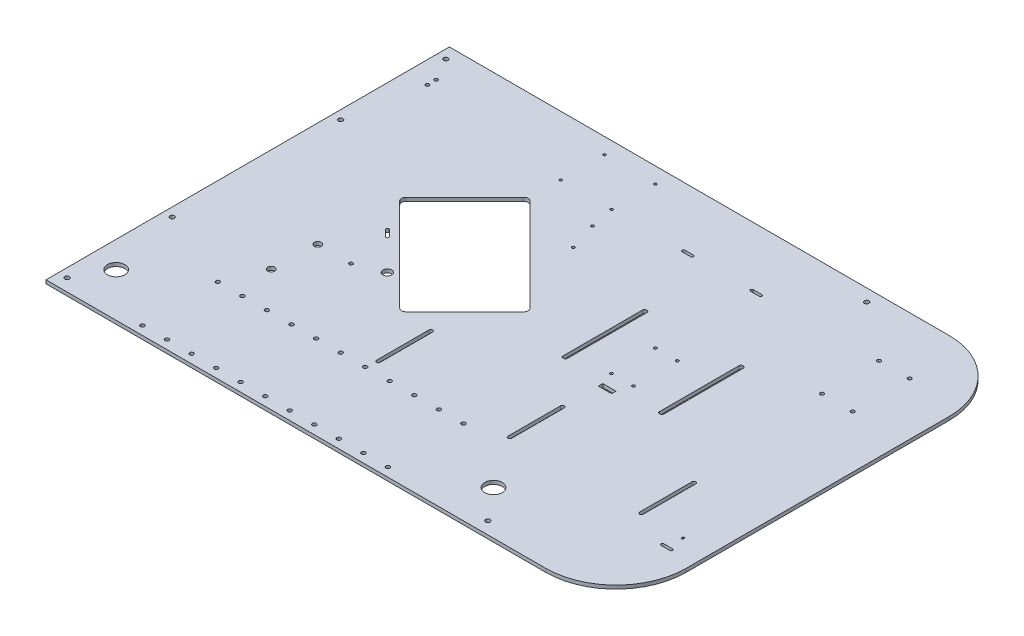
SolidWorks part; units mm, degrees
ref_plane "前视基准面" through (0, 0, 0) normal (0, 0, 1) x (1, 0, 0)
ref_plane "上视基准面" through (0, 0, 0) normal (0, 1, 0) x (1, 0, 0)
ref_plane "右视基准面" through (0, 0, 0) normal (1, 0, 0) x (0, 0, -1)
sketch "草图1" plane through (0, 0, 0) normal (0, 1, 0) x (1, 0, 0)
  line L1 (-325, 230) -> (325, 230)
  line L2 (-325, 230) -> (-325, -230)
  line L3 (-325, -230) -> (325, -230)
  line L4 (325, 230) -> (325, -230)
  line L5 (-325, 230) -> (325, -230) construction
  line L6 (-325, -230) -> (325, 230) construction
  point P0 (0, 0)
  dimension "D1" = 650
  dimension "D2" = 460
extrude "凸台-拉伸1" add sketch "草图1" along normal blind 4
sketch "草图2" plane through (0, 4, 0) normal (0, 1, 0) x (1, 0, 0)
  line L0 (325, -110) -> (145.735, -110) construction
  line L1 (325, -230) -> (325, 230) construction
  line L2 (288.7, -75) -> (319, -75) construction
  line L3 (-325, -230) -> (325, -230) construction
  line L4 (-152.45, -61.9939) -> (-152.45, -234.8498) construction
  line L5 (-241.4703, -110) -> (-123.3197, -110) construction
  circle A0 centre (319, -145) radius 2
  circle A1 centre (288.7, -145) radius 2
  circle A2 centre (319, -75) radius 2
  circle A3 centre (288.7, -75) radius 2
  circle A5 centre (-138.045, -75) radius 1.6
  circle A6 centre (-166.855, -75) radius 1.6
  circle A7 centre (-138.045, -145) radius 1.6
  circle A8 centre (-166.855, -145) radius 1.6
  dimension "D1" = 4
  dimension "D2" = 4
  dimension "D8" = 28.81
  dimension "D3" = 30.3
  dimension "D4" = 6
  dimension "D5" = 70
  dimension "D6" = 120
  dimension "D7" = 477.45
  dimension "D9" = 70
sketch "草图3" plane through (0, 4, 0) normal (0, 1, 0) x (1, 0, 0)
  line L0 (325, -230) -> (325, 230) construction
  line L1 (325, 230) -> (-325, 230) construction
  line L2 (230, 165) -> (265, 165) construction
  line L3 (230, 100) -> (265, 100) construction
  line L4 (230, 165) -> (230, 100) construction
  circle A0 centre (230, 165) radius 2.05
  circle A1 centre (265, 165) radius 2.05
  circle A2 centre (265, 100) radius 2.05
  circle A3 centre (230, 100) radius 2.05
  dimension "D1" = 4.1
  dimension "D2" = 4.1
  dimension "D3" = 4.1
  dimension "D4" = 4.1
  dimension "D5" = 35
  dimension "D6" = 65
  dimension "D7" = 35
  dimension "D8" = 60
  dimension "D9" = 65
extrude "切除-拉伸2" cut sketch "草图3" against normal through all
sketch "草图4" plane through (0, 4, 0) normal (0, 1, 0) x (1, 0, 0)
  line L0 (-325, 230) -> (-86.9477, -8.0523) construction
  line L5 (325, 230) -> (-325, 230) construction
  line L12 (-204.7918, 53.2233) -> (-130.5456, 127.4695)
  line L13 (-130.5456, 127.4695) -> (-17.4086, 14.3324)
  line L14 (-17.4086, 14.3324) -> (-91.6548, -59.9138)
  line L15 (-91.6548, -59.9138) -> (-204.7918, 53.2233)
  dimension "D1" = 45
  dimension "D2" = 65
  dimension "D3" = 40
  dimension "D4" = 160
  dimension "D5" = 210
extrude "切除-大方孔" cut sketch "草图4" against normal through all
sketch "草图5" plane through (0, 4, 0) normal (0, 1, 0) x (1, 0, 0)
  line L0 (-315, 216) -> (-315, 96) construction
  line L1 (-315, -96) -> (-315, -216) construction
  line L2 (-325, -230) -> (325, -230) construction
  line L3 (-325, 230) -> (325, -230) construction
  line L4 (0, 0) -> (0, 241.7531) construction
  line L5 (-325, 230) -> (-325, -230) construction
  line L6 (325, 230) -> (-325, 230) construction
  circle A4 centre (165, -216) radius 2.6
  circle A5 centre (-315, -216) radius 2.6
  circle A6 centre (-315, 216) radius 2.6
  circle A7 centre (165, 216) radius 2.6
  circle A8 centre (-315, 96) radius 2.6
  circle A9 centre (-315, -96) radius 2.6
  dimension "D1" = 5.2
  dimension "D2" = 5.2
  dimension "D3" = 5.2
  dimension "D4" = 5.2
  dimension "D5" = 5.2
  dimension "D6" = 5.2
  dimension "D7" = 120
  dimension "D8" = 120
  dimension "D9" = 14
  dimension "D10" = 10
  dimension "D11" = 14
  dimension "D12" = 10
extrude "切除-下层平板安装孔" cut sketch "草图5" against normal through all
fillet "圆角1" radius 80 1 edges at (325, 2, -230)
sketch "草图6" plane through (0, 4, 0) normal (0, 1, 0) x (1, 0, 0)
  line L0 (10, 162) -> (20, 162) construction
  line L1 (10, 163.6) -> (20, 163.6)
  line L2 (10, 160.4) -> (20, 160.4)
  line L3 (88, 162) -> (98, 162) construction
  line L4 (88, 163.6) -> (98, 163.6)
  line L5 (88, 160.4) -> (98, 160.4)
  line L6 (245, 230) -> (-325, 230) construction
  line L7 (-325, 230) -> (-325, -230) construction
  arc A2 (10, 163.6) -> (10, 160.4) centre (10, 162) ccw
  arc A3 (20, 160.4) -> (20, 163.6) centre (20, 162) ccw
  arc A4 (88, 163.6) -> (88, 160.4) centre (88, 162) ccw
  arc A5 (98, 160.4) -> (98, 163.6) centre (98, 162) ccw
  point P2 (15, 162)
  point P9 (93, 162)
  dimension "D1" = 1.6
  dimension "D2" = 1.6
  dimension "D3" = 10
  dimension "D4" = 10
  dimension "D5" = 78
  dimension "D6" = 68
  dimension "D7" = 340
extrude "切除-开关电源安装孔" cut sketch "草图6" against normal through all
sketch "草图7" plane through (0, 4, 0) normal (0, 1, 0) x (1, 0, 0)
  line L0 (245, -61) -> (245, -121) construction
  line L1 (247.1, -61) -> (247.1, -121)
  line L2 (242.9, -61) -> (242.9, -121)
  line L3 (95, -61) -> (95, -121) construction
  line L4 (97.1, -61) -> (97.1, -121)
  line L5 (92.9, -61) -> (92.9, -121)
  line L6 (-55, -61) -> (-55, -121) construction
  line L7 (-52.9, -61) -> (-52.9, -121)
  line L8 (-57.1, -61) -> (-57.1, -121)
  line L9 (-325, -230) -> (325, -230) construction
  line L10 (95, -91) -> (245, -91) construction
  line L11 (-55, -91) -> (95, -91) construction
  line L12 (325, -230) -> (325, 150) construction
  arc A0 (247.1, -61) -> (242.9, -61) centre (245, -61) ccw
  arc A1 (242.9, -121) -> (247.1, -121) centre (245, -121) ccw
  arc A2 (97.1, -61) -> (92.9, -61) centre (95, -61) ccw
  arc A3 (92.9, -121) -> (97.1, -121) centre (95, -121) ccw
  arc A4 (-52.9, -61) -> (-57.1, -61) centre (-55, -61) ccw
  arc A5 (-57.1, -121) -> (-52.9, -121) centre (-55, -121) ccw
  point P2 (245, -91)
  point P9 (95, -91)
  point P14 (-55, -91)
  dimension "D1" = 2.1
  dimension "D2" = 2.1
  dimension "D3" = 2.1
  dimension "D4" = 60
  dimension "D5" = 60
  dimension "D6" = 60
  dimension "D7" = 139
  dimension "D8" = 80
  dimension "D9" = 150
  dimension "D10" = 150
extrude "切除-长导轨安装孔" cut sketch "草图7" against normal through all
sketch "草图8" plane through (0, 4, 0) normal (0, 1, 0) x (1, 0, 0)
  line L0 (245, 230) -> (-325, 230) construction
  line L1 (-325, 230) -> (-325, -230) construction
  circle A0 centre (-130, 212) radius 1.5
  circle A1 centre (-72, 212) radius 1.5
  circle A2 centre (-72, 162) radius 1.5
  circle A3 centre (-130, 162) radius 1.5
  dimension "D1" = 3
  dimension "D2" = 3
  dimension "D3" = 3
  dimension "D4" = 3
  dimension "D5" = 50
  dimension "D6" = 50
  dimension "D7" = 58
  dimension "D8" = 58
  dimension "D9" = 18
  dimension "D10" = 195
extrude "切除-树莓派安装孔" cut sketch "草图8" against normal through all
sketch "草图9" plane through (0, 4, 0) normal (0, 1, 0) x (1, 0, 0)
  line L0 (-325, 230) -> (-325, -230) construction
  line L1 (-325, -230) -> (325, -230) construction
  circle A0 centre (-225, -220) radius 2.25
  circle A1 centre (-197, -220) radius 2.25
  circle A2 centre (-169, -220) radius 2.25
  circle A3 centre (-141, -220) radius 2.25
  circle A4 centre (-113, -220) radius 2.25
  circle A5 centre (-85, -220) radius 2.25
  circle A6 centre (-57, -220) radius 2.25
  circle A7 centre (-29, -220) radius 2.25
  circle A8 centre (-1, -220) radius 2.25
  circle A9 centre (27, -220) radius 2.25
  circle A10 centre (55, -220) radius 2.25
  circle A11 centre (-197, -134) radius 2.25
  circle A12 centre (-169, -134) radius 2.25
  circle A13 centre (-141, -134) radius 2.25
  circle A14 centre (-113, -134) radius 2.25
  circle A15 centre (-85, -134) radius 2.25
  circle A16 centre (-57, -134) radius 2.25
  circle A17 centre (-29, -134) radius 2.25
  circle A18 centre (-1, -134) radius 2.25
  circle A19 centre (27, -134) radius 2.25
  circle A20 centre (55, -134) radius 2.25
  circle A21 centre (-225, -134) radius 2.25
  dimension "D1" = 4.5
  dimension "D2" = 100
  dimension "D3" = 10
  dimension "D4" = 11
  dimension "D5" = 2
extrude "切除-步进电机驱动安装孔" cut sketch "草图9" against normal through all
fillet "圆角2" radius 80 1 edges at (325, 2, 230)
sketch "草图10" plane through (0, 4, 0) normal (0, 1, 0) x (1, 0, 0)
  line L0 (90, 50) -> (115, 50) construction
  line L1 (115, 50) -> (115, 0) construction
  line L2 (115, 0) -> (90, 0) construction
  line L3 (90, 0) -> (90, 50) construction
  line L4 (-325, -230) -> (245, -230) construction
  line L5 (325, -150) -> (325, 150) construction
  line L6 (60, 85) -> (60, -15) construction
  line L7 (60, -15) -> (145, -15) construction
  line L8 (145, -15) -> (145, 85) construction
  line L9 (145, 85) -> (60, 85) construction
  line L10 (102.5, 50) -> (102.5, 0) construction
  line L12 (50, 82.5) -> (45, 82.5)
  line L13 (50, 82.5) -> (50, -12.5)
  line L14 (50, -12.5) -> (45, -12.5)
  line L15 (45, 82.5) -> (45, -12.5)
  line L16 (155, 82.5) -> (160, 82.5)
  line L17 (155, 82.5) -> (155, -12.5)
  line L18 (155, -12.5) -> (160, -12.5)
  line L19 (160, 82.5) -> (160, -12.5)
  circle A0 centre (115, 50) radius 1.6
  circle A1 centre (115, 0) radius 1.6
  circle A2 centre (90, 0) radius 1.6
  circle A3 centre (90, 50) radius 1.6
  point P26 (47.5, 82.5)
  dimension "D1" = 3.2
  dimension "D2" = 3.2
  dimension "D3" = 3.2
  dimension "D4" = 3.2
  dimension "D5" = 50
  dimension "D6" = 25
  dimension "D7" = 230
  dimension "D8" = 210
  dimension "D9" = 100
  dimension "D10" = 85
  dimension "D11" = 42.5
  dimension "D12" = 5
  dimension "D13" = 5
  dimension "D14" = 95
  dimension "D15" = 95
  dimension "D16" = 2.5
  dimension "D17" = 2.5
  dimension "D18" = 15
  dimension "D19" = 10
  dimension "D20" = 10
extrude "切除-电路板安装孔" cut sketch "草图10" against normal through all
fillet "圆角3" radius 5 4 edges at (-17.4086, 2, -14.3324) (-91.6548, 2, 59.9138) (-204.7918, 2, -53.2233) (-130.5456, 2, -127.4695)
fillet "圆角4" radius 2 8 edges at (160, 2, -82.5) (155, 2, -82.5) (155, 2, 12.5) (160, 2, 12.5) (50, 2, 12.5) (45, 2, 12.5) (50, 2, -82.5) (45, 2, -82.5)
sketch "草图11" plane through (0, 4, 0) normal (0, 1, 0) x (1, 0, 0)
  line L2 (288, -140) -> (298, -140) construction
  line L3 (288, -138.4) -> (298, -138.4)
  line L4 (288, -141.6) -> (298, -141.6)
  line L5 (325, -150) -> (325, 150) construction
  line L6 (-325, -230) -> (245, -230) construction
  line L8 (292.2625, -120.5) -> (294.2625, -120.5)
  line L9 (292.2625, -120.5) -> (292.2625, -123.5)
  line L10 (292.2625, -123.5) -> (294.2625, -123.5)
  line L11 (294.2625, -120.5) -> (294.2625, -123.5)
  line L12 (292.2625, -120.5) -> (294.2625, -123.5) construction
  line L13 (292.2625, -123.5) -> (294.2625, -120.5) construction
  arc A1 (288, -138.4) -> (288, -141.6) centre (288, -140) ccw
  arc A2 (298, -141.6) -> (298, -138.4) centre (298, -140) ccw
  point P2 (293, -140)
  point P11 (293.2625, -122)
  dimension "D1" = 1.6
  dimension "D2" = 10
  dimension "D3" = 32
  dimension "D4" = 90
  dimension "D5" = 2
  dimension "D6" = 3
  dimension "D7" = 18
extrude "切除-长导轨限位开关安装孔" cut sketch "草图11" against normal through all
sketch "草图12" plane through (0, 4, 0) normal (0, 1, 0) x (1, 0, 0)
  line L2 (-180.0431, 14.3324) -> (-172.972, 7.2614) construction
  line L3 (-178.9117, 15.4638) -> (-171.8407, 8.3927)
  line L4 (-181.1745, 13.2011) -> (-174.1034, 6.13)
  line L5 (-201.2563, 49.6878) -> (-95.1903, -56.3782) construction
  line L6 (-134.0812, 123.934) -> (-201.2563, 56.7588) construction
  arc A1 (-178.9117, 15.4638) -> (-181.1745, 13.2011) centre (-180.0431, 14.3324) ccw
  arc A2 (-174.1034, 6.13) -> (-171.8407, 8.3927) centre (-172.972, 7.2614) ccw
  point P2 (-176.5076, 10.7969)
  dimension "D1" = 1.6
  dimension "D2" = 10
  dimension "D3" = 50
  dimension "D4" = 10
extrude "切除-下面导轨限位开关安装孔" cut sketch "草图12" against normal through all
sketch "草图13" plane through (0, 4, 0) normal (0, 1, 0) x (1, 0, 0)
  line L1 (95, -15) -> (110, -15)
  line L2 (95, -15) -> (95, -20)
  line L3 (95, -20) -> (110, -20)
  line L4 (110, -15) -> (110, -20)
  line L5 (90, 0) -> (115, 0) construction
  line L6 (102.5, 0) -> (102.5, -15) construction
  dimension "D1" = 5
  dimension "D2" = 15
  dimension "D3" = 15
extrude "切除-限位开关接线孔" cut sketch "草图13" against normal through all
sketch "草图14" plane through (0, 4, 0) normal (0, 1, 0) x (1, 0, 0)
  line L0 (-285, 159.5242) -> (-285, -100) construction
  line L1 (-325, 230) -> (-325, -230) construction
  line L2 (-325, -230) -> (245, -230) construction
  text T0 "<b>TWB</b>" font "Consolas" height 20
  dimension "D1" = 40
  dimension "D2" = 130
sketch "草图15" plane through (0, 4, 0) normal (0, 1, 0) x (1, 0, 0)
  line L0 (-325, 230) -> (-325, -230) construction
  line L1 (-205, -40) -> (-167, -40) construction
  line L2 (-325, -230) -> (245, -230) construction
  circle A0 centre (-167, -40) radius 2
  circle A1 centre (-205, -40) radius 4
  dimension "D1" = 8
  dimension "D2" = 4
  dimension "D3" = 120
  dimension "D4" = 38
  dimension "D5" = 190
extrude "切除-长导轨走线孔" cut sketch "草图15" against normal through all
sketch "草图16" plane through (0, 4, 0) normal (0, 1, 0) x (1, 0, 0)
  line L0 (-201.2563, 49.6878) -> (-95.1903, -56.3782) construction
  line L1 (-88.1192, -56.3782) -> (-20.9441, 10.7969) construction
  line L2 (-325, -230) -> (245, -230) construction
  line L3 (-325, 230) -> (-325, -230) construction
  line L4 (-295, -180) -> (135.3864, -180) construction
  line L5 (-57.1, -91) -> (-207.1, -91) construction
  line L6 (-57.1, -61) -> (-57.1, -121) construction
  circle A0 centre (-137.6167, -28.094) radius 5
  circle A1 centre (-295, -180) radius 10
  circle A2 centre (135.3864, -180) radius 10
  circle A3 centre (-207.1, -91) radius 4
  dimension "D1" = 10
  dimension "D4" = 20
  dimension "D7" = 20
  dimension "D8" = 8
  dimension "D2" = 10
  dimension "D3" = 55
  dimension "D5" = 50
  dimension "D6" = 30
  dimension "D9" = 150
extrude "切除-拉伸12" cut sketch "草图16" against normal through all
sketch "草图17" plane through (0, 4, 0) normal (0, 1, 0) x (1, 0, 0)
  line L0 (-300, 190) -> (-300, 180) construction
  line L1 (-300, 190) -> (-300, 230) construction
  line L2 (245, 230) -> (-325, 230) construction
  line L3 (-325, 230) -> (-325, -230) construction
  circle A0 centre (-300, 190) radius 2
  circle A1 centre (-300, 180) radius 2
  dimension "D1" = 4
  dimension "D2" = 4
  dimension "D3" = 40
  dimension "D4" = 10
  dimension "D5" = 25
extrude "切除-拉伸13" cut sketch "草图17" against normal through all
sketch "草图18" plane through (0, 4, 0) normal (0, 1, 0) x (1, 0, 0)
  line L0 (-77.5126, 123.934) -> (-56.2994, 102.7208) construction
  line L1 (-56.2994, 102.7208) -> (-45.3393, 113.6809) construction
  line L2 (-45.3393, 113.6809) -> (-66.5525, 134.8941) construction
  line L3 (-66.5525, 134.8941) -> (-77.5126, 123.934) construction
  line L4 (-20.9441, 17.868) -> (-127.0101, 123.934) construction
  line L5 (-134.0812, 123.934) -> (-201.2563, 56.7588) construction
  circle A2 centre (-66.5525, 134.8941) radius 1.6
  circle A3 centre (-56.2994, 102.7208) radius 1.6
  point P2 (-66.906, 113.3274)
  dimension "D1" = 30
  dimension "D2" = 15.5
  dimension "D5" = 3.2
  dimension "D6" = 3.2
  dimension "D3" = 35
  dimension "D4" = 70
extrude "切除-拉伸14" cut sketch "草图18" against normal through all
